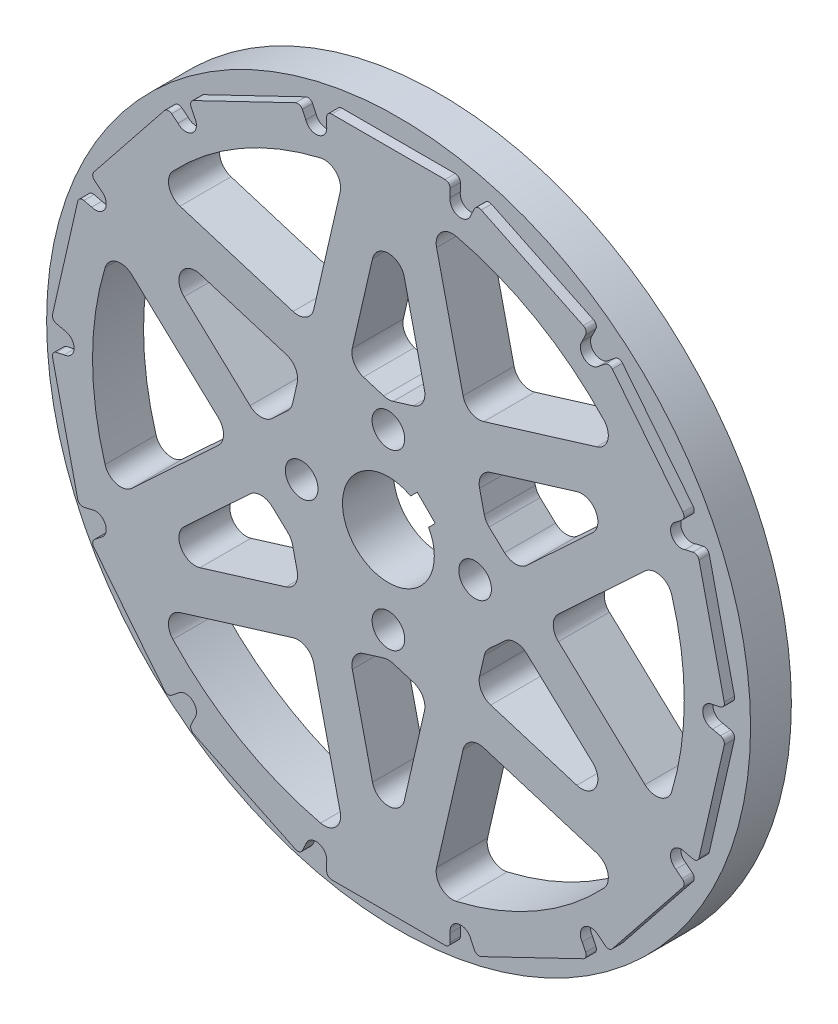
SolidWorks part; units mm, degrees
material "2018 合金"
ref_plane "正面" through (0, 0, 0) normal (0, 0, 1) x (1, 0, 0)
ref_plane "平面" through (0, 0, 0) normal (0, 1, 0) x (1, 0, 0)
ref_plane "右側面" through (0, 0, 0) normal (1, 0, 0) x (0, 0, -1)
sketch "ｽｹｯﾁ1" plane through (0, 0, 0) normal (0, 0, 1) x (1, 0, 0)
  circle A0 centre (0, 0) radius 34.5
  dimension "D1" = 69
extrude "ﾎﾞｽ - 押し出し1" add sketch "ｽｹｯﾁ1" along normal blind 4
sketch "ｽｹｯﾁ2" plane through (0, 0, 4) normal (0, 0, 1) x (1, 0, 0)
  circle A0 centre (0, 0) radius 31.5
  circle A1 centre (0, 0) radius 34.5 construction
  dimension "D1" = 3
extrude "ﾎﾞｽ - 押し出し2" add sketch "ｽｹｯﾁ2" along normal blind 1
sketch "ｽｹｯﾁ3" plane through (0, 0, 4) normal (0, 0, 1) x (1, 0, 0)
  line L1 (-6.05, 30.5) -> (6.05, 30.5)
  line L2 (-6.05, 30.5) -> (-6.05, 32.5)
  line L3 (-6.05, 32.5) -> (6.05, 32.5)
  line L4 (6.05, 30.5) -> (6.05, 32.5)
  line L5 (-6.05, 30.5) -> (6.05, 32.5) construction
  line L6 (-6.05, 32.5) -> (6.05, 30.5) construction
  circle A0 centre (0, 0) radius 31.5 construction
  point P0 (0, 31.5)
  dimension "D1" = 12.1
  dimension "D2" = 1
extrude "ﾎﾞｽ - 押し出し3" add sketch "ｽｹｯﾁ3" along normal blind 1
pattern_circular "円形ﾊﾟﾀｰﾝ1" count 14 over 360 about axis through (0, 0, 0) along (0, 0, 1) of "ﾎﾞｽ - 押し出し3"
sketch "ｽｹｯﾁ5" plane through (0, 0, 5) normal (0, 0, 1) x (1, 0, 0)
  line L0 (-7.0895, 31.0613) -> (0, 0) construction
  circle A0 centre (-7.0895, 31.0613) radius 1.05
  arc A1 (-6.05, 30.9135) -> (-7.962, 30.4771) centre (0, 0) ccw construction
  point P6 (-7.0094, 30.7102)
  dimension "D1" = 2.1
extrude "ｶｯﾄ - 押し出し1" cut sketch "ｽｹｯﾁ5" against normal blind 1
pattern_circular "円形ﾊﾟﾀｰﾝ2" count 14 over 360 about axis through (0, 0, 0) along (0, 0, 1) of "ｶｯﾄ - 押し出し1"
sketch "ｽｹｯﾁ6" plane through (0, 0, 5) normal (0, 0, 1) x (1, 0, 0)
  circle A0 centre (0, 0) radius 4.5
  dimension "D1" = 9
extrude "ｶｯﾄ - 押し出し2" cut sketch "ｽｹｯﾁ6" against normal through all
sketch "ｽｹｯﾁ7" plane through (0, 0, 5) normal (0, 0, 1) x (1, 0, 0)
  circle A0 centre (0, 0) radius 10.5
  circle A1 centre (0, 0) radius 29
  circle A2 centre (0, 0) radius 4.5 construction
  dimension "D1" = 58
  dimension "D2" = 6
extrude "ｶｯﾄ - 押し出し3" cut sketch "ｽｹｯﾁ7" against normal through all and the other way through all
sketch "ｽｹｯﾁ8" plane through (0, 0, 5) normal (0, 0, 1) x (1, 0, 0)
  line L0 (-10.2329, 2.3534) -> (-4.1739, 28.6981)
  line L1 (0, 29) -> (-4.4863, 9.4933)
  line L2 (0, 0) -> (0, 29) construction
  circle A0 centre (0, 0) radius 10.5 construction
  circle A1 centre (0, 0) radius 29 construction
  arc A2 (0, 29) -> (-4.1739, 28.6981) centre (0, 0) ccw
  arc A3 (-4.4863, 9.4933) -> (-10.2329, 2.3534) centre (0, 0) ccw
  dimension "D1" = 4
extrude "ﾎﾞｽ - 押し出し4" add sketch "ｽｹｯﾁ8" against normal up to surface (5 mm away) up to face at (4.5, 0, 0)
pattern_circular "円形ﾊﾟﾀｰﾝ3" count 6 over 360 about axis through (0, 0, 0) along (0, 0, 1) of "ﾎﾞｽ - 押し出し4"
mirror "ﾐﾗｰ1" about plane through (0, 0, 0) normal (1, 0, 0) of "円形ﾊﾟﾀｰﾝ3", "ﾎﾞｽ - 押し出し4"
fillet "ﾌｨﾚｯﾄ1" radius 0.5 2 edges at (-33.0314, -1.3336, 4.5) (-30.3389, -13.1302, 4.5)
fillet "ﾌｨﾚｯﾄ2" radius 0.5 26 edges at (-8.6504, -31.9065, 4.5) (-6.05, -32.5, 4.5) (6.05, -32.5, 4.5) (8.6504, -31.9065, 4.5) (19.5521, -26.6565, 4.5) (21.6374, -24.9935, 4.5) (29.1816, -15.5333, 4.5) (30.3389, -13.1302, 4.5) (33.0314, -1.3336, 4.5) (33.0314, 1.3336, 4.5) (30.3389, 13.1302, 4.5) (29.1816, 15.5333, 4.5) (21.6374, 24.9935, 4.5) (19.5521, 26.6565, 4.5) (8.6504, 31.9065, 4.5) (6.05, 32.5, 4.5) (-6.05, 32.5, 4.5) (-8.6504, 31.9065, 4.5) (-19.5521, 26.6565, 4.5) (-21.6374, 24.9935, 4.5) (-29.1816, 15.5333, 4.5) (-30.3389, 13.1302, 4.5) (-33.0314, 1.3336, 4.5) (-19.5521, -26.6565, 4.5) (-21.6374, -24.9935, 4.5) (-29.1816, -15.5333, 4.5)
sketch "ｽｹｯﾁ9" plane through (0, 0, 5) normal (0, 0, 1) x (1, 0, 0)
  circle A0 centre (0, 0) radius 8.5 construction
  circle A1 centre (-8.5, 0) radius 1.6
  circle A2 centre (0, 8.5) radius 1.6
  circle A3 centre (8.5, 0) radius 1.6
  circle A4 centre (0, -8.5) radius 1.6
  dimension "D1" = 17
  dimension "D2" = 3.2
extrude "ｶｯﾄ - 押し出し4" cut sketch "ｽｹｯﾁ9" against normal through all
sketch "ｽｹｯﾁ10" plane through (0, 0, 5) normal (0, 0, 1) x (1, 0, 0)
  line L0 (0, 0) -> (2.8284, 2.8284) construction
  line L1 (0, 0) -> (0, 4) construction
  line L3 (1.0607, 2.8284) -> (2.8284, 1.0607)
  line L4 (1.0607, 2.8284) -> (2.8284, 4.5962)
  line L5 (2.8284, 4.5962) -> (4.5962, 2.8284)
  line L6 (2.8284, 1.0607) -> (4.5962, 2.8284)
  line L7 (1.0607, 2.8284) -> (4.5962, 2.8284) construction
  line L8 (2.8284, 4.5962) -> (2.8284, 1.0607) construction
  circle A0 centre (0, 0) radius 4 construction
  dimension "D1" = 8
  dimension "D2" = 45
  dimension "D3" = 2.5
  dimension "D4" = 2.5
extrude "ｶｯﾄ - 押し出し5" cut sketch "ｽｹｯﾁ10" against normal through all
fillet "ﾌｨﾚｯﾄ3" radius 1.6 24 edges at (4.1739, -28.6981, 2.5) (22.7663, -17.9637, 2.5) (7.7049, -13.3452, 2.5) (25.1147, -14.5, 2.5) (8.6037, -9.437, 2.5) (9.5112, -5.4913, 2.5) (12.4745, -2.7325, 2.5) (26.9402, -10.7344, 2.5) (26.9402, 10.7344, 2.5) (15.4097, 0, 2.5) (12.4745, 2.7325, 2.5) (25.1147, 14.5, 2.5) (9.5112, 5.4913, 2.5) (8.6037, 9.437, 2.5) (4.1739, 28.6981, 2.5) (22.7663, 17.9637, 2.5) (7.7049, 13.3452, 2.5) (3.8708, 12.1695, 2.5) (0, 10.9826, 2.5) (0, 29, 2.5) (-3.8708, 12.1695, 2.5) (-22.7663, 17.9637, 2.5) (-7.7049, 13.3452, 2.5) (-4.1739, 28.6981, 2.5)
fillet "ﾌｨﾚｯﾄ4" radius 1.6 18 edges at (-25.1147, 14.5, 2.5) (-8.6037, 9.437, 2.5) (-9.5112, 5.4913, 2.5) (-12.4745, 2.7325, 2.5) (-26.9402, -10.7344, 2.5) (-26.9402, 10.7344, 2.5) (-15.4097, 0, 2.5) (-25.1147, -14.5, 2.5) (-12.4745, -2.7325, 2.5) (-9.5112, -5.4913, 2.5) (-8.6037, -9.437, 2.5) (-22.7663, -17.9637, 2.5) (-7.7049, -13.3452, 2.5) (-4.1739, -28.6981, 2.5) (0, -29, 2.5) (-3.8708, -12.1695, 2.5) (0, -10.9826, 2.5) (3.8708, -12.1695, 2.5)
